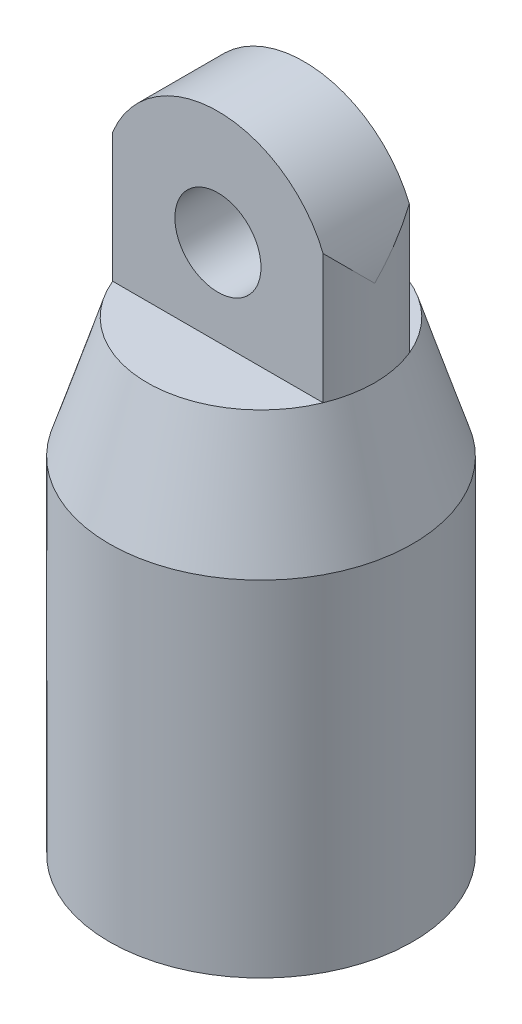
SolidWorks part; units mm, degrees
ref_plane "Front Plane" through (0, 0, 0) normal (0, 0, 1) x (1, 0, 0)
ref_plane "Top Plane" through (0, 0, 0) normal (0, 1, 0) x (1, 0, 0)
ref_plane "Right Plane" through (0, 0, 0) normal (1, 0, 0) x (0, 0, -1)
sketch "Sketch1" plane through (0, 0, 0) normal (0, 1, 0) x (1, 0, 0)
  circle A0 centre (0, 0) radius 4.572
  circle A2 centre (0, 0) radius 5.588
extrude "Boss-Extrude1" add sketch "Sketch1" along normal blind 12.7
sketch "Sketch2" plane through (0, 0, 0) normal (0, 0, 1) x (1, 0, 0)
  line L20 (-5.588, 12.7) -> (-4.572, 12.7)
  line L22 (4.572, 12.7) -> (-4.572, 12.7) construction
  line L23 (-4.572, 12.7) -> (-2.159, 15.113)
  line L24 (-2.159, 15.113) -> (0, 15.113)
  line L25 (0, 15.113) -> (0, 17.145)
  line L26 (0, 17.145) -> (-2.159, 17.145)
  line L28 (-2.159, 17.145) -> (-4.191, 17.145)
  line L29 (-4.191, 17.145) -> (-5.588, 12.7)
revolve "Revolve2" add sketch "Sketch2" angle 360 about L25
sketch "Sketch3" plane through (0, 0, 0) normal (0, 0, 1) x (1, 0, 0)
  line L14 (-4.191, 17.145) -> (4.191, 17.145)
  line L15 (4.191, 17.145) -> (-4.191, 17.145) construction
  line L16 (4.191, 17.145) -> (4.191, 20.32)
  line L17 (-4.191, 17.145) -> (-4.191, 20.32)
  circle A4 centre (0, 20.32) radius 1.5875
  arc A5 (-4.191, 20.32) -> (4.191, 20.32) centre (0, 20.32) cw
extrude "Boss-Extrude3" add sketch "Sketch3" along normal mid plane 3.175
sketch "Sketch6" plane through (0, 17.145, 0) normal (0, -1, 0) x (1, 0, 0)
  circle A0 centre (0, 0) radius 4.191
extrude "Cut-Extrude4" cut sketch "Sketch6" against normal blind 25.4 flip side to cut
